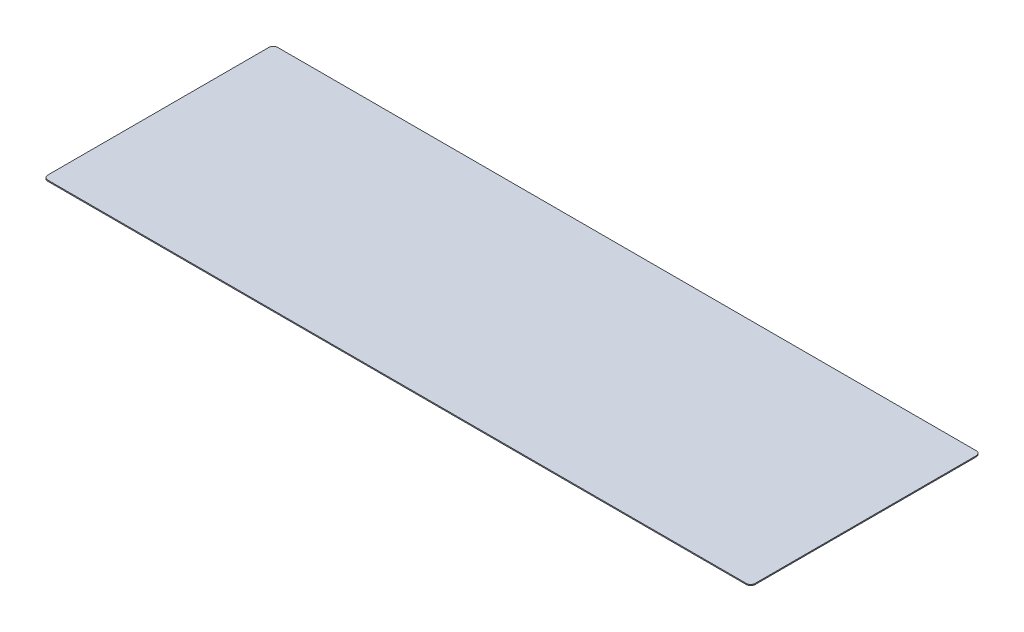
SolidWorks part; units mm, degrees
ref_plane "Front" through (0, 0, 0) normal (0, 0, 1) x (1, 0, 0)
ref_plane "Top" through (0, 0, 0) normal (0, 1, 0) x (1, 0, 0)
ref_plane "Right" through (0, 0, 0) normal (1, 0, 0) x (0, 0, -1)
sketch "Sketch1" plane through (0, 0, 0) normal (0, 1, 0) x (1, 0, 0)
  line L1 (6.35, 0) -> (1009.65, 0)
  line L2 (0, 6.35) -> (0, 323.85)
  line L3 (6.35, 330.2) -> (1009.65, 330.2)
  line L4 (1016, 6.35) -> (1016, 323.85)
  line L5 (0, 0) -> (1016, 330.2) construction
  line L6 (0, 330.2) -> (1016, 0) construction
  arc A0 (1009.65, 330.2) -> (1016, 323.85) centre (1009.65, 323.85) cw
  arc A1 (1009.65, 0) -> (1016, 6.35) centre (1009.65, 6.35) ccw
  arc A2 (6.35, 0) -> (0, 6.35) centre (6.35, 6.35) cw
  arc A3 (0, 323.85) -> (6.35, 330.2) centre (6.35, 323.85) cw
  point P4 (508, 165.1)
  dimension "D3" = 6.35
  dimension "D1" = 330.2
  dimension "D2" = 1016
extrude "Boss-Extrude1" add sketch "Sketch1" along normal blind 1.524
